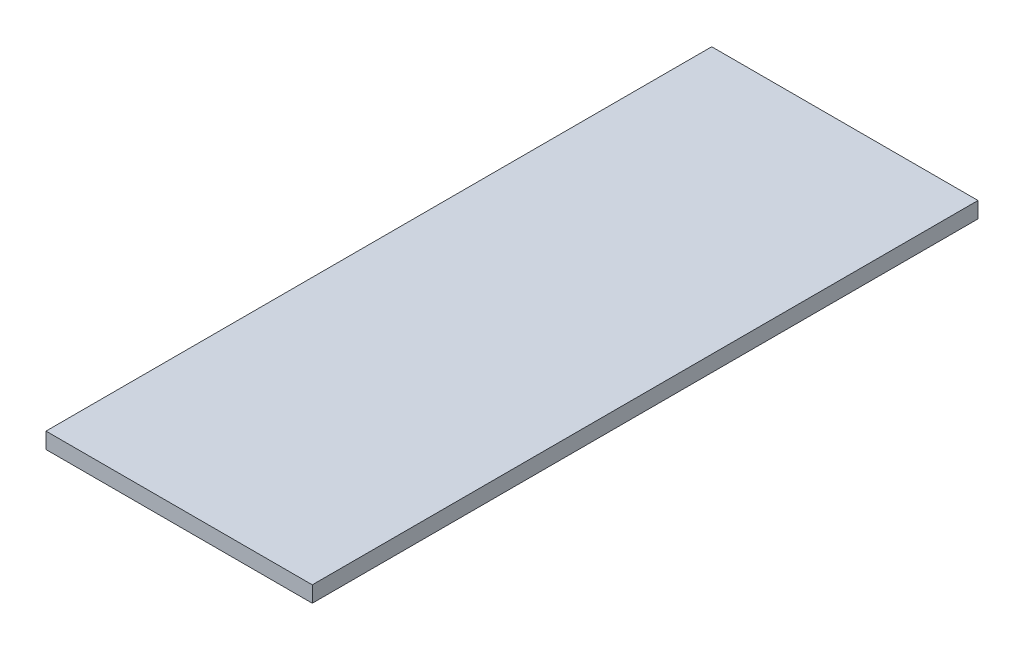
SolidWorks part; units mm, degrees
ref_plane "Front Plane" through (0, 0, 0) normal (0, 0, 1) x (1, 0, 0)
ref_plane "Top Plane" through (0, 0, 0) normal (0, 1, 0) x (1, 0, 0)
ref_plane "Right Plane" through (0, 0, 0) normal (1, 0, 0) x (0, 0, -1)
sketch "Sketch1" plane through (0, 0, 0) normal (0, 1, 0) x (1, 0, 0)
  line L1 (-25, 62.5) -> (25, 62.5)
  line L2 (-25, 62.5) -> (-25, -62.5)
  line L3 (-25, -62.5) -> (25, -62.5)
  line L4 (25, 62.5) -> (25, -62.5)
  line L5 (-25, 62.5) -> (25, -62.5) construction
  line L6 (-25, -62.5) -> (25, 62.5) construction
  point P0 (0, 0)
  dimension "D1" = 125
  dimension "D2" = 50
extrude "Boss-Extrude1" add sketch "Sketch1" along normal blind 3
